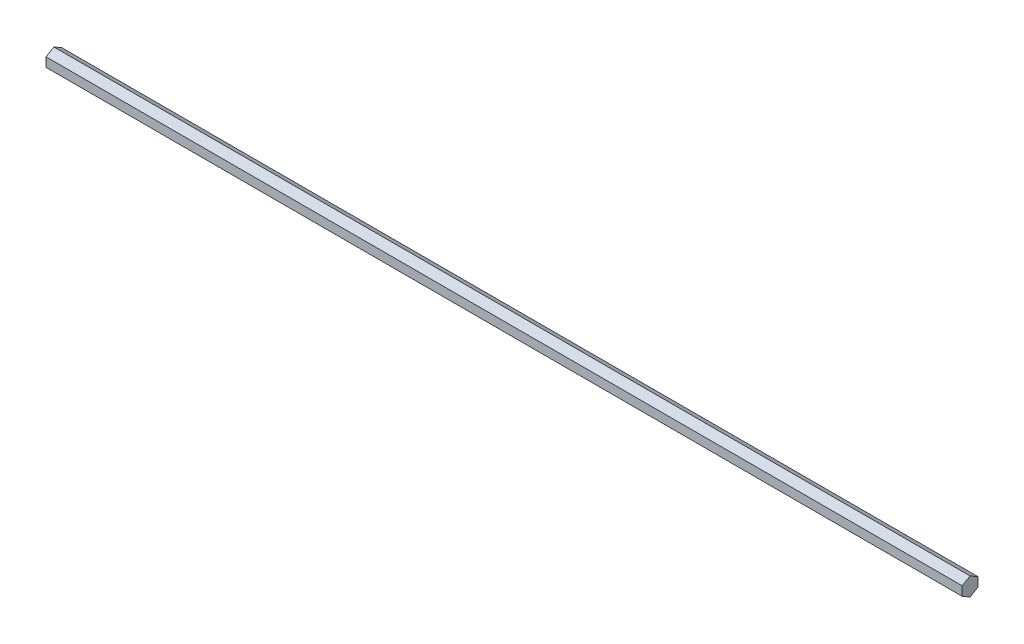
SolidWorks part; units mm, degrees
ref_plane "Front" through (0, 0, 0) normal (0, 0, 1) x (1, 0, 0)
ref_plane "Top" through (0, 0, 0) normal (0, 1, 0) x (1, 0, 0)
ref_plane "Right" through (0, 0, 0) normal (1, 0, 0) x (0, 0, -1)
sketch "Sketch1" plane through (0, 0, 0) normal (1, 0, 0) x (0, 0, -1)
  line L1 (0, 7.3323) -> (-6.35, 3.6662)
  line L2 (-6.35, 3.6662) -> (-6.35, -3.6662)
  line L3 (-6.35, -3.6662) -> (0, -7.3323)
  line L4 (0, -7.3323) -> (6.35, -3.6662)
  line L5 (6.35, -3.6662) -> (6.35, 3.6662)
  line L6 (6.35, 3.6662) -> (0, 7.3323)
  circle A0 centre (0, 0) radius 6.35 construction
  dimension "D1" = 12.7
extrude "Boss-Extrude1" add sketch "Sketch1" along normal blind 736.6
